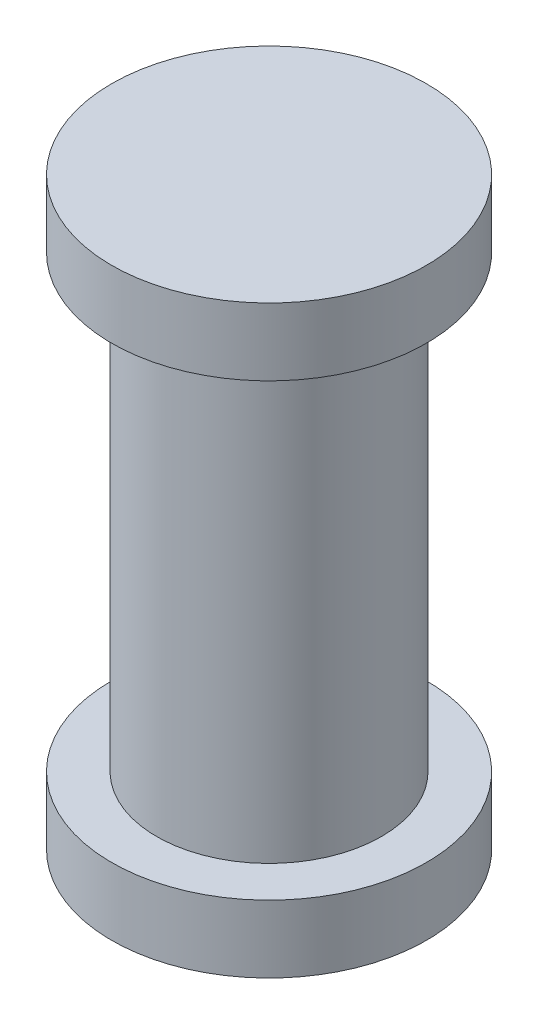
SolidWorks part; units mm, degrees
ref_plane "Front Plane" through (0, 0, 0) normal (0, 0, 1) x (1, 0, 0)
ref_plane "Top Plane" through (0, 0, 0) normal (0, 1, 0) x (1, 0, 0)
ref_plane "Right Plane" through (0, 0, 0) normal (1, 0, 0) x (0, 0, -1)
sketch "Sketch1" plane through (0, 0, 0) normal (0, 0, 1) x (1, 0, 0)
  line L0 (0, 0) -> (7, 0)
  line L1 (7, 0) -> (7, 3)
  line L2 (7, 3) -> (5, 3)
  line L3 (5, 3) -> (5, 23)
  line L4 (5, 23) -> (7, 23)
  line L5 (7, 23) -> (7, 26)
  line L6 (7, 26) -> (0, 26)
  line L7 (0, 26) -> (0, 0)
  dimension "D1" = 5
  dimension "D2" = 7
  dimension "D3" = 20
  dimension "D4" = 3
revolve "Revolve1" add sketch "Sketch1" angle 360 about L7
